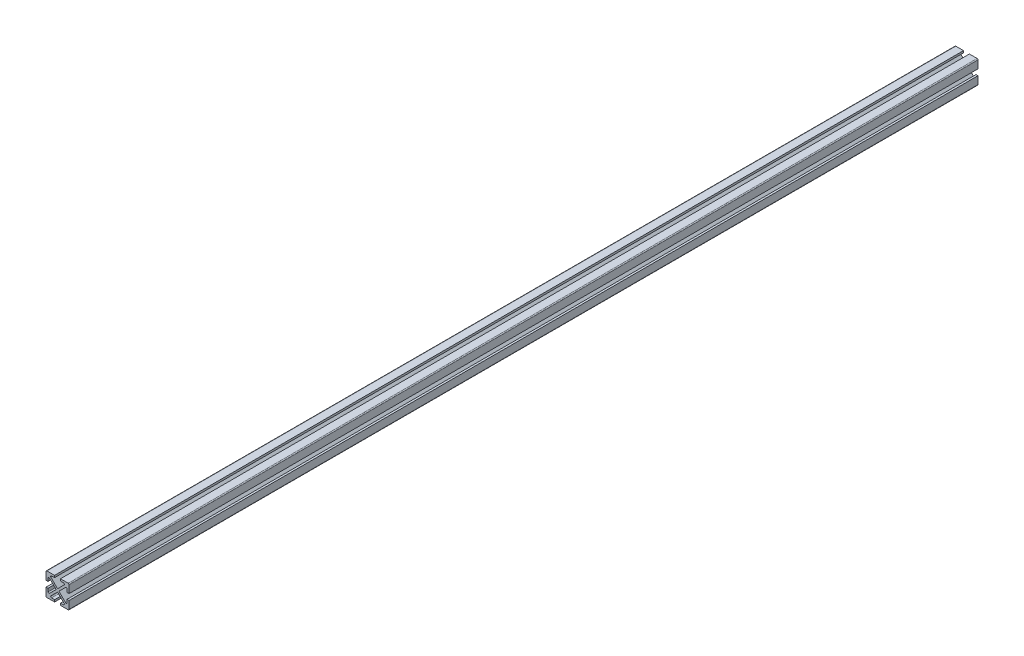
SolidWorks part; units mm, degrees
material "6061 Alloy"
ref_plane "Front Plane" through (0, 0, 0) normal (0, 0, 1) x (1, 0, 0)
ref_plane "Top Plane" through (0, 0, 0) normal (0, 1, 0) x (1, 0, 0)
ref_plane "Right Plane" through (0, 0, 0) normal (1, 0, 0) x (0, 0, -1)
sketch "Sketch1" plane through (0, 0, 0) normal (0, 0, 1) x (1, 0, 0)
  line L0 (-3.2512, 12.7) -> (-3.2512, 10.4902)
  line L9 (-12.7, -12.7) -> (12.7, -12.7)
  line L10 (-12.7, -12.7) -> (-12.7, 12.7)
  line L11 (-12.7, 12.7) -> (12.7, 12.7)
  line L12 (12.7, -12.7) -> (12.7, 12.7)
  line L13 (-12.7, -12.7) -> (12.7, 12.7) construction
  line L14 (-12.7, 12.7) -> (12.7, -12.7) construction
  line L17 (3.2512, 10.4902) -> (3.2512, 12.7)
  line L18 (0, 0) -> (0, 12.7) construction
  line L19 (-3.2512, 12.7) -> (3.2512, 12.7)
  line L20 (-8.9276, 10.4902) -> (0, 1.5626)
  line L21 (0, 1.5626) -> (8.9276, 10.4902)
  line L22 (8.9276, 10.4902) -> (3.2512, 10.4902)
  line L23 (-8.9276, 10.4902) -> (-3.2512, 10.4902)
  line L24 (10.4902, 8.9276) -> (10.4902, 3.2512)
  line L25 (12.7, 3.2512) -> (10.4902, 3.2512)
  line L26 (12.7, 3.2512) -> (12.7, -3.2512)
  line L27 (10.4902, -3.2512) -> (12.7, -3.2512)
  line L28 (10.4902, -8.9276) -> (10.4902, -3.2512)
  line L29 (1.5626, 0) -> (10.4902, -8.9276)
  line L30 (10.4902, 8.9276) -> (1.5626, 0)
  line L31 (8.9276, -10.4902) -> (3.2512, -10.4902)
  line L32 (3.2512, -12.7) -> (3.2512, -10.4902)
  line L33 (3.2512, -12.7) -> (-3.2512, -12.7)
  line L34 (-3.2512, -10.4902) -> (-3.2512, -12.7)
  line L35 (-8.9276, -10.4902) -> (-3.2512, -10.4902)
  line L36 (0, -1.5626) -> (-8.9276, -10.4902)
  line L37 (8.9276, -10.4902) -> (0, -1.5626)
  line L38 (-10.4902, -8.9276) -> (-10.4902, -3.2512)
  line L39 (-12.7, -3.2512) -> (-10.4902, -3.2512)
  line L40 (-12.7, -3.2512) -> (-12.7, 3.2512)
  line L41 (-10.4902, 3.2512) -> (-12.7, 3.2512)
  line L42 (-10.4902, 8.9276) -> (-10.4902, 3.2512)
  line L43 (-1.5626, 0) -> (-10.4902, 8.9276)
  line L44 (-10.4902, -8.9276) -> (-1.5626, 0)
  point P0 (0, 0)
  point P41 (0, 0)
  dimension "D1" = 25.4
  dimension "D2" = 6.5024
  dimension "D3" = 2.2098
  dimension "D4" = 2.2098
  dimension "D5" = 4
extrude "Boss-Extrude1" add sketch "Sketch1" along normal mid plane 1000 contours L44 L38 L39 L10 L9 L34 L35 L36 L37 L31 L32 L12 L27 L28 L29 L30 L24 L25 L11 L17 L22 L21 L20 L23 L0 L41 L42 L43
fillet "Fillet1" radius 1 12 edges at (10.4902, 8.9276, 0) (8.9276, 10.4902, 0) (10.4902, -8.9276, 0) (8.9276, -10.4902, 0) (-8.9276, -10.4902, 0) (-10.4902, -8.9276, 0) (-10.4902, 8.9276, 0) (-8.9276, 10.4902, 0) (-12.7, -12.7, 0) (12.7, -12.7, 0) (12.7, 12.7, 0) (-12.7, 12.7, 0)
